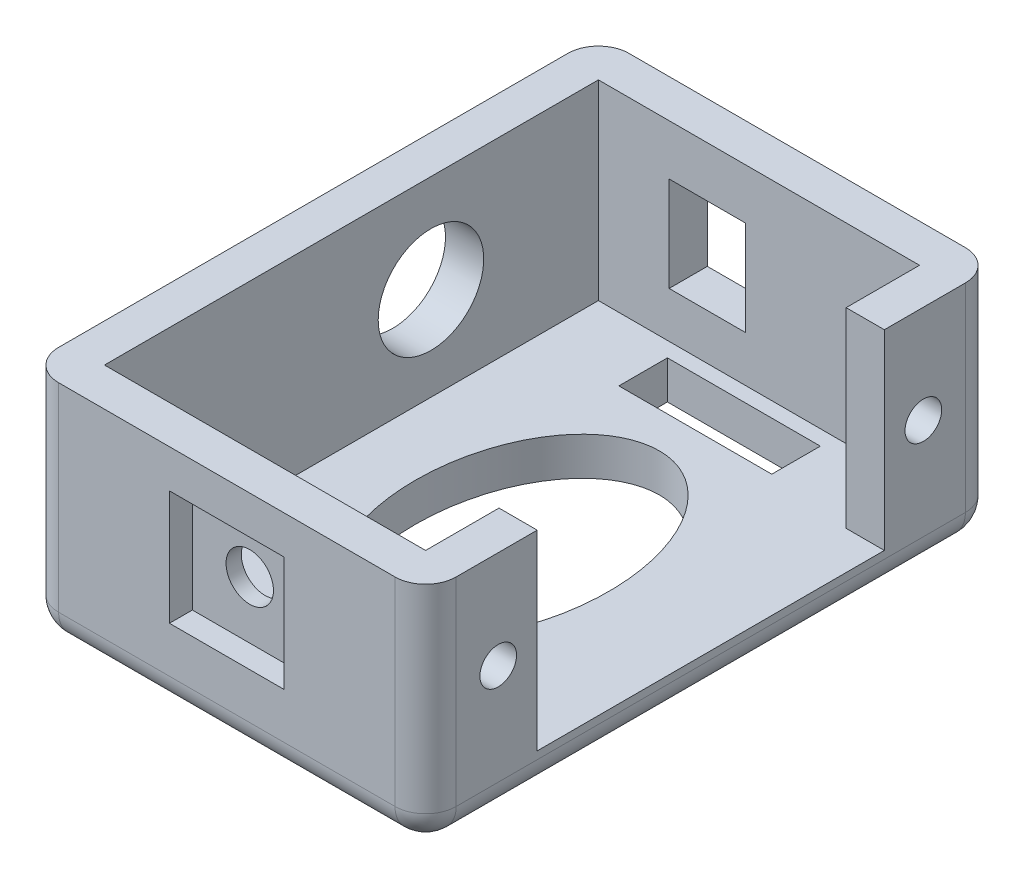
SolidWorks part; units mm, degrees
ref_plane "Front Plane" through (0, 0, 0) normal (0, 0, 1) x (1, 0, 0)
ref_plane "Top Plane" through (0, 0, 0) normal (0, 1, 0) x (1, 0, 0)
ref_plane "Right Plane" through (0, 0, 0) normal (1, 0, 0) x (0, 0, -1)
sketch "Sketch1" plane through (0, 0, 0) normal (0, 1, 0) x (1, 0, 0)
  line L1 (0, 29.9941) -> (-26, 29.9941)
  line L2 (-26, 29.9941) -> (-26, -7.3059)
  line L3 (-26, -7.3059) -> (0, -7.3059)
  line L4 (0, -7.3059) -> (0, -0.0059)
  line L5 (0, -0.0059) -> (-2.5, -0.0059)
  line L6 (-2.5, -0.0059) -> (-2.5, -4.8059)
  line L7 (-2.5, -4.8059) -> (-23.5, -4.8059)
  line L8 (-23.5, -4.8059) -> (-23.5, 27.4941)
  line L11 (0, 22.6941) -> (-2.5, 22.6941)
  line L13 (0, 29.9941) -> (0, 22.6941)
  line L14 (-23.5, 27.4941) -> (-2.5, 27.4941)
  line L15 (-2.5, 27.4941) -> (-2.5, 22.6941)
  dimension "D1" = 4.8
  dimension "D2" = 2.5
  dimension "D3" = 2.5
  dimension "D4" = 2.5
  dimension "D5" = 21
  dimension "D6" = 37.3
extrude "Boss-Extrude1" add sketch "Sketch1" along normal blind 15
sketch "Sketch2" plane through (-23.5, 0, 0) normal (1, 0, 0) x (0, 0, -1)
  line L5 (27.4941, 15) -> (27.4941, 0) construction
  line L6 (-4.8059, 0) -> (27.4941, 0)
  line L7 (-4.8059, 0) -> (-4.8059, 2.5)
  line L8 (-4.8059, 2.5) -> (27.4941, 2.5)
  line L9 (27.4941, 0) -> (27.4941, 2.5)
  dimension "D1" = 2.5
extrude "Boss-Extrude2" add sketch "Sketch2" along normal through all
sketch "Sketch3" plane through (0, 0, -29.9941) normal (0, 0, -1) x (-1, 0, 0)
  line L0 (26, 15) -> (26, 0) construction
  line L1 (13.875, 11.7) -> (18.875, 11.7)
  line L2 (13.875, 11.7) -> (13.875, 5.5)
  line L3 (13.875, 5.5) -> (18.875, 5.5)
  line L4 (18.875, 11.7) -> (18.875, 5.5)
  line L5 (0, 0) -> (26, 0) construction
  dimension "D1" = 6.2
  dimension "D2" = 5
  dimension "D3" = 7.125
  dimension "D4" = 5.5
extrude "Cut-Extrude1" cut sketch "Sketch3" against normal blind 12.5
sketch "Sketch4" plane through (-26, 0, 0) normal (-1, 0, 0) x (0, 0, 1)
  line L0 (-29.9941, 15) -> (7.3059, 15) construction
  line L1 (-29.9941, 15) -> (-29.9941, 0) construction
  circle A0 centre (-16.5441, 8.6) radius 3.45
  dimension "D1" = 6.9
  dimension "D2" = 6.4
  dimension "D3" = 13.45
extrude "Cut-Extrude2" cut sketch "Sketch4" against normal up to next
sketch "Sketch5" plane through (0, 0, 0) normal (1, 0, 0) x (0, 0, -1)
  line L0 (-0.0059, 15) -> (-0.0059, 2.5) construction
  line L1 (-7.3059, 15) -> (-0.0059, 15) construction
  circle A0 centre (-2.5559, 8.6) radius 1.2
  dimension "D2" = 2.4
  dimension "D1" = 2.55
  dimension "D3" = 6.4
extrude "Cut-Extrude3" cut sketch "Sketch5" against normal up to next (2.5 mm away)
ref_plane "Plane1" through (0, 0, -11.3441) normal (0, 0, 1) x (1, 0, 0)
mirror "Mirror1" about plane through (0, 0, -11.3441) normal (0, 0, 1) of "Cut-Extrude3"
sketch "Sketch6" plane through (0, 0, 7.3059) normal (0, 0, 1) x (1, 0, 0)
  line L0 (-2.5, 15) -> (-2.5, 2.5) construction
  line L1 (-23.5, 15) -> (-23.5, 2.5) construction
  line L2 (-2.5, 15) -> (-2.5, 2.5) construction
  line L3 (-23.5, 15) -> (-23.5, 2.5) construction
  line L4 (-23.5, 8.75) -> (-19, 8.75) construction
  line L5 (-19, 8.75) -> (-13, 8.75) construction
  line L6 (-13, 8.75) -> (-7, 8.75) construction
  line L7 (-7, 8.75) -> (-2.5, 8.75) construction
  circle A1 centre (-13, 8.75) radius 1.55
  dimension "D1" = 3.1
  dimension "D2" = 4.5
extrude "Cut-Extrude4" cut sketch "Sketch6" against normal up to next
fillet "Fillet2" radius 2 8 edges at (0, 0, -11.3441) (-13, 0, -29.9941) (-26, 0, -11.3441) (0, 7.5, -29.9941) (-26, 7.5, -29.9941) (0, 7.5, 7.3059) (-26, 7.5, 7.3059) (-13, 0, 7.3059)
sketch "Sketch7" plane through (0, 0, 7.3059) normal (0, 0, 1) x (1, 0, 0)
  line L1 (-16.75, 12.5) -> (-9.25, 12.5)
  line L2 (-16.75, 12.5) -> (-16.75, 5)
  line L3 (-16.75, 5) -> (-9.25, 5)
  line L4 (-9.25, 12.5) -> (-9.25, 5)
  circle A0 centre (-13, 8.75) radius 1.55 construction
  circle A1 centre (-13, 8.75) radius 1.55
  point P8 (-13, 12.5)
  point P10 (-9.25, 8.75)
  dimension "D1" = 7.5
extrude "Cut-Extrude5" cut sketch "Sketch7" against normal blind 1.5
sketch "Sketch8" plane through (0, 2.5, 0) normal (0, 1, 0) x (1, 0, 0)
  line L0 (-13, 1.7101) -> (-13, 11.3441) construction
  line L1 (-13, 11.3441) -> (-19.3129, 11.3441) construction
  line L2 (-13, -0.6439) -> (-13, 1.7101) construction
  line L3 (-8, -3.8189) -> (-18, -3.8189)
  line L4 (-2.5, -0.0059) -> (-13, -0.0059) construction
  line L5 (-13, -0.0059) -> (-23.5, -0.0059) construction
  line L6 (-23.5, 27.4941) -> (-23.5, -4.8059) construction
  line L7 (-8, -3.8189) -> (-8, -0.6439)
  line L8 (-8, -0.6439) -> (-18, -0.6439)
  line L9 (-18, -3.8189) -> (-18, -0.6439)
  line L10 (-8, 23.3321) -> (-18, 23.3321)
  line L11 (-8, 23.3321) -> (-8, 26.5071)
  line L12 (-8, 26.5071) -> (-18, 26.5071)
  line L13 (-18, 23.3321) -> (-18, 26.5071)
  line L14 (-13, 20.9781) -> (-13, 23.3321) construction
  line L15 (-13, 26.5071) -> (-13, 27.4941) construction
  line L16 (-2.5, 27.4941) -> (-23.5, 27.4941) construction
  line L17 (-1.375, 11.3441) -> (1.375, 11.3441) construction
  line L18 (-13, -3.8189) -> (-13, -4.8059) construction
  line L19 (-2.5, -4.8059) -> (-23.5, -4.8059) construction
  ellipse E3 centre (-13, 11.3441) end of major axis (-13, 20.9781) minor radius 6.3129
  point P15 (-13, 23.3321)
  point P16 (-13, -0.6439)
  dimension "D1" = 3.175
  dimension "D2" = 10
extrude "Cut-Extrude6" cut sketch "Sketch8" against normal up to next
